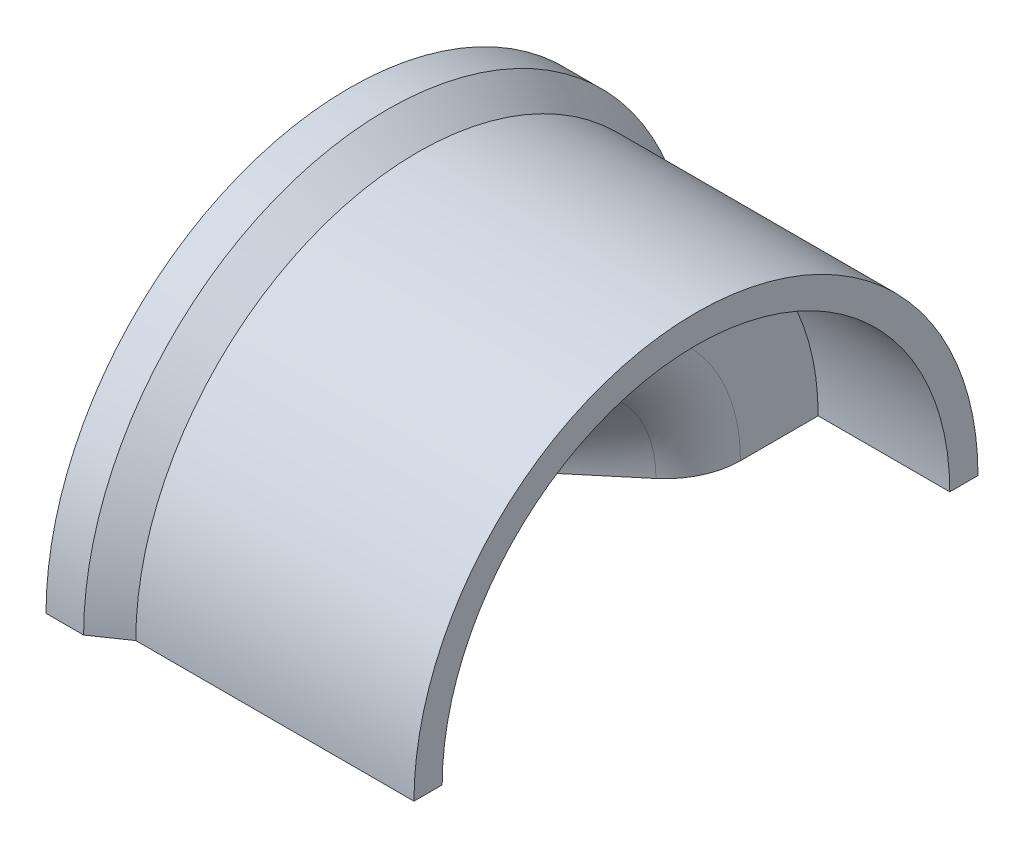
SolidWorks part; units mm, degrees
ref_plane "Front Plane" through (0, 0, 0) normal (0, 0, 1) x (1, 0, 0)
ref_plane "Top Plane" through (0, 0, 0) normal (0, 1, 0) x (1, 0, 0)
ref_plane "Right Plane" through (0, 0, 0) normal (1, 0, 0) x (0, 0, -1)
sketch "Sketch1" plane through (0, 0, 0) normal (0, 1, 0) x (1, 0, 0)
  line L16 (28.575, 0) -> (31.9094, 0) construction
  line L17 (22.4605, 20.4867) -> (19.9205, 20.4867)
  line L23 (22.4605, 20.4867) -> (31.9094, 13.9813)
  line L31 (31.9094, 13.9813) -> (31.9094, 0)
  line L32 (28.575, 0) -> (31.9094, 0)
  arc A5 (28.575, 0) -> (19.9205, 20.4867) centre (0, 0) ccw
revolve "Revolve4" add sketch "Sketch1" angle 360 about L16
sketch "Sketch5" plane through (31.9094, 0, 0) normal (1, 0, 0) x (0, 0, -1)
  circle A2 centre (0, 0) radius 19.05
extrude "Boss-Extrude1" add sketch "Sketch5" along normal blind 11.43
sketch "Sketch11" plane through (43.3394, 0, 0) normal (1, 0, 0) x (0, 0, -1)
  circle A2 centre (0, 0) radius 17.145
sketch "Sketch12" plane through (31.9094, 0, 0) normal (-1, 0, 0) x (0, 0, 1)
  circle A1 centre (0, 0) radius 19.05
extrude "Boss-Extrude4" add sketch "Sketch12" along normal up to next contours A1
extrude "Cut-Extrude5" cut sketch "Sketch11" against normal blind 8.89
sketch "Sketch13" plane through (34.4494, 0, 0) normal (1, 0, 0) x (0, 0, -1)
  circle A0 centre (0, 0) radius 9.525
extrude "Cut-Extrude7" cut sketch "Sketch13" against normal blind 6.35 draft 40
sketch "Sketch14" plane through (43.3394, 0, 0) normal (1, 0, 0) x (0, 0, -1)
  line L1 (-21.6639, 0) -> (22.4409, 0)
  line L2 (-21.6639, 0) -> (-21.6639, -21.7416)
  line L3 (-21.6639, -21.7416) -> (22.4409, -21.7416)
  line L4 (22.4409, 0) -> (22.4409, -21.7416)
extrude "Cut-Extrude8" cut sketch "Sketch14" against normal through all both and the other way through all
fillet "Fillet6" radius 5.08 1 edges at (34.4494, 9.525, 0)
